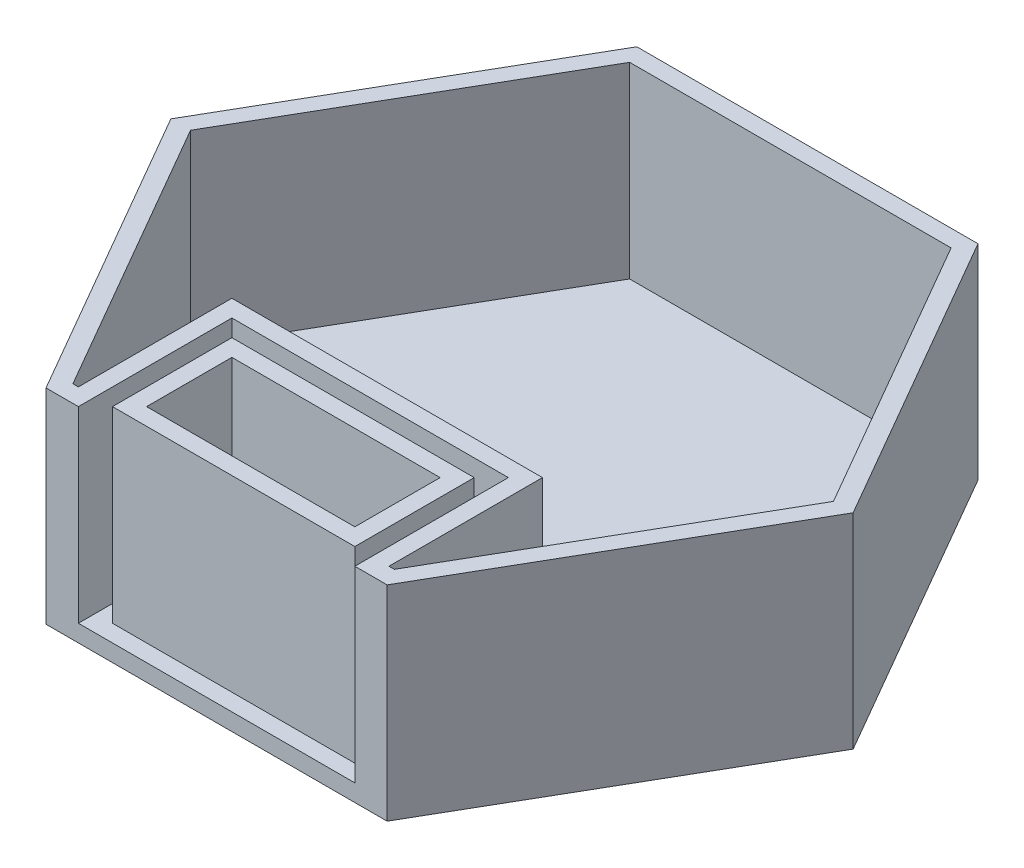
SolidWorks part; units mm, degrees
ref_plane "Front Plane" through (0, 0, 0) normal (0, 0, 1) x (1, 0, 0)
ref_plane "Top Plane" through (0, 0, 0) normal (0, 1, 0) x (1, 0, 0)
ref_plane "Right Plane" through (0, 0, 0) normal (1, 0, 0) x (0, 0, -1)
sketch "Sketch2" plane through (0, 0, 0) normal (0, 1, 0) x (1, 0, 0)
  line L0 (0, 0) -> (153.0899, 0) construction
  line L1 (76.2, 0) -> (101.6, 43.9941)
  line L2 (101.6, 43.9941) -> (76.2, 87.9882)
  line L3 (76.2, 87.9882) -> (25.4, 87.9882)
  line L4 (25.4, 87.9882) -> (0, 43.9941)
  line L5 (0, 43.9941) -> (25.4, 0)
  line L6 (25.4, 0) -> (76.2, 0)
  line L7 (0, 0) -> (0, 103.6086) construction
  circle A0 centre (50.8, 43.9941) radius 43.9941 construction
  dimension "D1" = 50.8
extrude "Boss-Extrude1" add sketch "Sketch2" along normal blind 2.54
sketch "Sketch3" plane through (0, 0, 0) normal (0, 1, 0) x (1, 0, 0)
  line L0 (25.4, 87.9882) -> (0, 43.9941)
  line L1 (0, 43.9941) -> (25.4, 0)
  line L3 (76.2, 0) -> (101.6, 43.9941)
  line L4 (101.6, 43.9941) -> (76.2, 87.9882)
  line L5 (76.2, 87.9882) -> (25.4, 87.9882)
  line L6 (26.8665, 85.4482) -> (2.9329, 43.9941)
  line L7 (2.9329, 43.9941) -> (26.8665, 2.54)
  line L9 (74.7335, 2.54) -> (98.6671, 43.9941)
  line L10 (98.6671, 43.9941) -> (74.7335, 85.4482)
  line L11 (74.7335, 85.4482) -> (26.8665, 85.4482)
  line L14 (30.2211, 22.86) -> (71.3908, 22.86)
  line L22 (32.7611, 20.32) -> (32.7611, 2.54)
  line L23 (32.7611, 2.54) -> (32.7611, 20.32)
  line L24 (68.8508, 20.32) -> (68.8508, 2.54)
  line L25 (32.7611, 2.54) -> (68.8508, 2.54)
  line L27 (35.3011, 17.78) -> (66.3108, 17.78)
  line L28 (35.3011, 17.78) -> (35.3011, 5.08)
  line L29 (35.3011, 5.08) -> (66.3108, 5.08)
  line L30 (32.7611, 20.32) -> (68.8508, 20.32)
  line L31 (26.8665, 2.54) -> (27.6811, 2.54)
  line L32 (27.6811, 2.54) -> (27.6811, 25.4)
  line L33 (27.6811, 25.4) -> (73.9308, 25.4)
  line L36 (25.4, 0) -> (76.2, 0) construction
  line L37 (30.2211, 0) -> (25.4, 0)
  line L39 (71.3908, 0) -> (76.2, 0)
  line L40 (71.3908, 22.86) -> (71.3908, 0)
  line L41 (30.2211, 22.86) -> (30.2211, 0)
  line L42 (73.9308, 25.4) -> (73.9308, 2.54)
  line L43 (73.9308, 2.54) -> (74.7335, 2.54)
  line L44 (66.3108, 17.78) -> (66.3108, 5.08)
  dimension "D1" = 2.54
  dimension "D2" = 2.54
  dimension "D3" = 2.54
  dimension "D4" = 2.54
  dimension "D5" = 2.54
  dimension "D6" = 2.54
  dimension "D7" = 2.54
  dimension "D8" = 2.54
  dimension "D9" = 2.54
  dimension "D10" = 2.54
  dimension "D11" = 2.54
  dimension "D12" = 2.54
  dimension "D13" = 2.54
  dimension "D14" = 2.54
  dimension "D15" = 2.54
  dimension "D16" = 25.4
  dimension "D17" = 2.54
extrude "Boss-Extrude2" add sketch "Sketch3" along normal blind 30.48 contours L30 L22 L25 L24 L27 L44 L29 L28 | L41 L14 L40 L39 L3 L4 L5 L0 L1 L37 L43 L42 L33 L32 L31 L7 L6 L11 L10 L9
